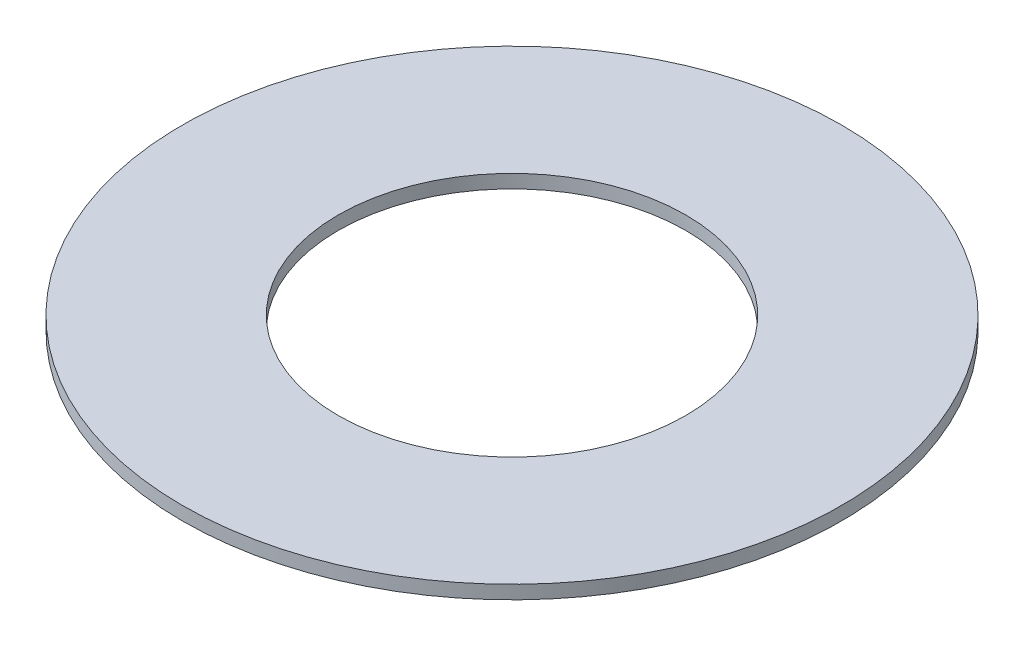
SolidWorks part; units mm, degrees
ref_plane "Front Plane" through (0, 0, 0) normal (0, 0, 1) x (1, 0, 0)
ref_plane "Top Plane" through (0, 0, 0) normal (0, 1, 0) x (1, 0, 0)
ref_plane "Right Plane" through (0, 0, 0) normal (1, 0, 0) x (0, 0, -1)
sketch "Sketch1" plane through (0, 0, 0) normal (0, 1, 0) x (1, 0, 0)
  circle A0 centre (0, 0) radius 11.6
  circle A1 centre (0, 0) radius 22
  dimension "D1" = 23.2
  dimension "D2" = 44
extrude "Boss-Extrude1" add sketch "Sketch1" along normal blind 0.9
